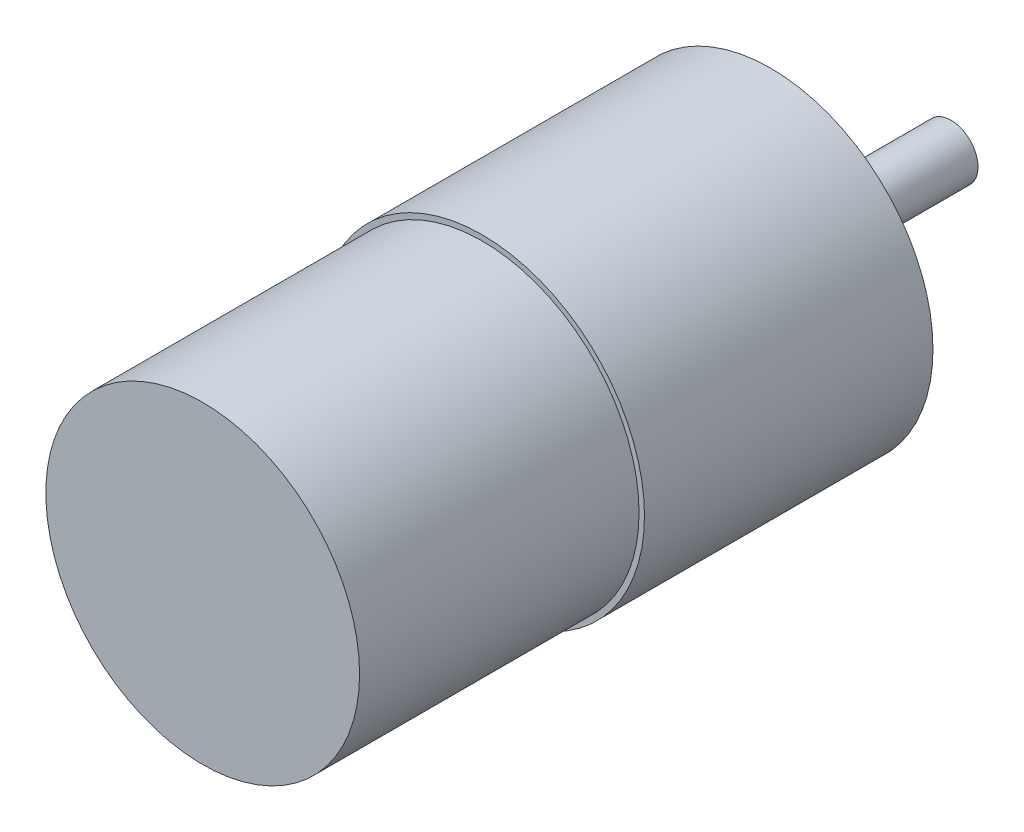
SolidWorks part; units mm, degrees
ref_plane "前视基准面" through (0, 0, 0) normal (0, 0, 1) x (1, 0, 0)
ref_plane "上视基准面" through (0, 0, 0) normal (0, 1, 0) x (1, 0, 0)
ref_plane "右视基准面" through (0, 0, 0) normal (1, 0, 0) x (0, 0, -1)
sketch "草图1" plane through (0, 0, 0) normal (0, 0, 1) x (1, 0, 0)
  circle A0 centre (0, 0) radius 18
  dimension "D1" = 36
extrude "凸台-拉伸1" add sketch "草图1" along normal blind 32
sketch "草图2" plane through (0, 0, 32) normal (0, 0, 1) x (1, 0, 0)
  circle A0 centre (0, 0) radius 17.4
  dimension "D1" = 34.8
extrude "凸台-拉伸2" add sketch "草图2" along normal blind 31
sketch "草图3" plane through (0, 0, 0) normal (0, 0, -1) x (-1, 0, 0)
  circle A0 centre (0, 0) radius 11
  dimension "D1" = 22
extrude "凸台-拉伸3" add sketch "草图3" along normal blind 2
sketch "草图4" plane through (0, 0, -2) normal (0, 0, -1) x (-1, 0, 0)
  circle A0 centre (0, 0) radius 4
  dimension "D1" = 8
extrude "凸台-拉伸4" add sketch "草图4" along normal blind 3
sketch "草图5" plane through (0, 0, -5) normal (0, 0, -1) x (-1, 0, 0)
  circle A0 centre (0, 0) radius 3
  dimension "D1" = 6
extrude "凸台-拉伸5" add sketch "草图5" along normal blind 15
sketch "草图6" plane through (0, 0, 0) normal (0, 0, -1) x (-1, 0, 0)
  circle A0 centre (0, 0) radius 14 construction
  circle A1 centre (0, 14) radius 1.5
  circle A2 centre (0, -14) radius 1.5
  circle A3 centre (14, 0) radius 1.5
  circle A4 centre (-14, 0) radius 1.5
  dimension "D1" = 28
  dimension "D2" = 3
extrude "切除-拉伸2" cut sketch "草图6" against normal blind 5 contours A0 | A4 | A1 | A3 | A2
